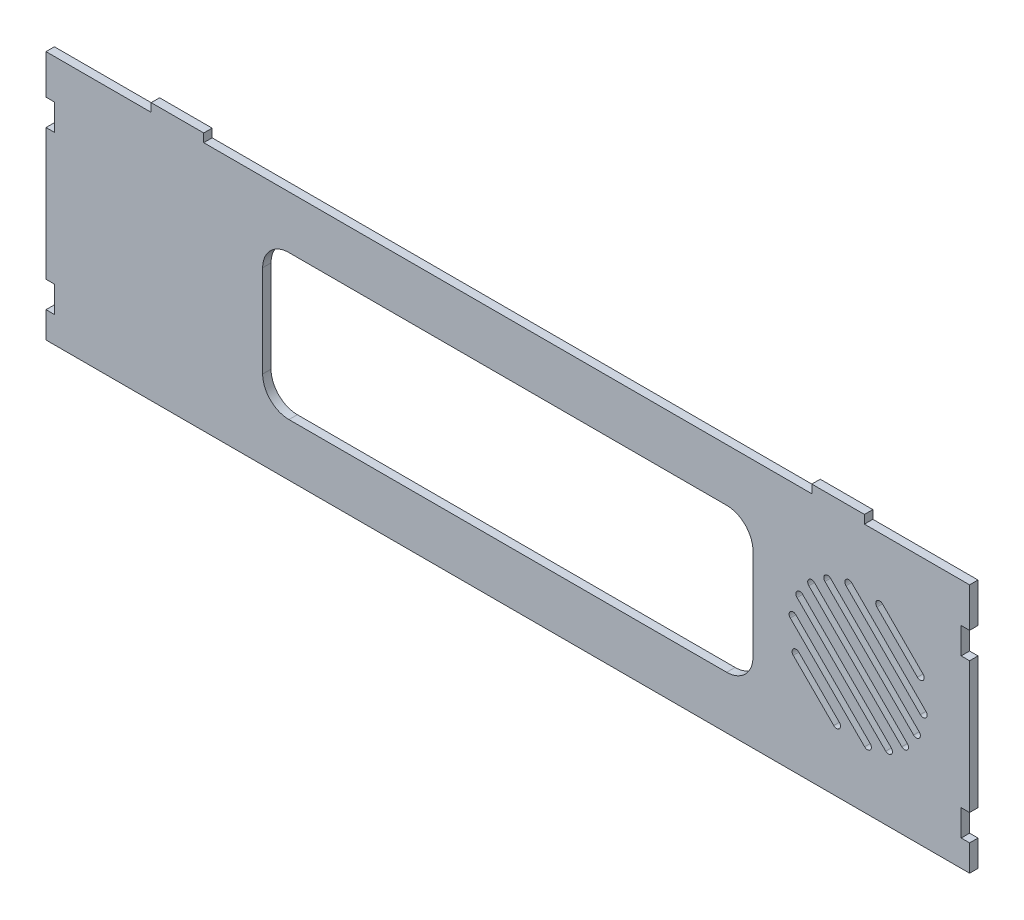
SolidWorks part; units mm, degrees
ref_plane "Front Plane" through (0, 0, 0) normal (0, 0, 1) x (1, 0, 0)
ref_plane "Top Plane" through (0, 0, 0) normal (0, 1, 0) x (1, 0, 0)
ref_plane "Right Plane" through (0, 0, 0) normal (1, 0, 0) x (0, 0, -1)
sketch "Sketch1" plane through (0, 0, 0) normal (0, 0, 1) x (1, 0, 0)
  line L0 (-223.0755, -19.05) -> (-219.0115, -19.05)
  line L1 (-223.0755, 0) -> (-172.2755, 0)
  line L2 (-223.0755, 0) -> (-223.0755, -19.05)
  line L3 (-223.0755, -120.65) -> (223.0755, -120.65)
  line L4 (223.0755, 0) -> (223.0755, -19.05)
  line L5 (-219.0115, -19.05) -> (-219.0115, -31.75)
  line L6 (-219.0115, -31.75) -> (-223.0755, -31.75)
  line L7 (-223.0755, -31.75) -> (-223.0755, -95.25)
  line L8 (-223.0755, -95.25) -> (-219.0115, -95.25)
  line L9 (-219.0115, -95.25) -> (-219.0115, -107.95)
  line L10 (-219.0115, -107.95) -> (-223.0755, -107.95)
  line L11 (223.0755, -19.05) -> (219.0115, -19.05)
  line L12 (219.0115, -19.05) -> (219.0115, -31.75)
  line L13 (219.0115, -31.75) -> (223.0755, -31.75)
  line L14 (223.0755, -95.25) -> (219.0115, -95.25)
  line L15 (219.0115, -95.25) -> (219.0115, -107.95)
  line L16 (219.0115, -107.95) -> (223.0755, -107.95)
  line L17 (-223.0755, -107.95) -> (-223.0755, -120.65)
  line L18 (223.0755, -107.95) -> (223.0755, -120.65)
  line L19 (223.0755, -31.75) -> (223.0755, -95.25)
  line L20 (223.0755, 4.064) -> (223.0755, 0) construction
  line L21 (-118.4275, -120.65) -> (-223.0755, -120.65) construction
  line L22 (-146.8755, 4.064) -> (-146.8755, 0) construction
  line L23 (-146.8755, 0) -> (146.8755, 0)
  line L24 (172.2755, 0) -> (172.2755, 4.064)
  line L25 (172.2755, 4.064) -> (146.8755, 4.064)
  line L26 (146.8755, 0) -> (146.8755, 4.064)
  line L28 (-146.8755, 0) -> (-146.8755, 4.064)
  line L29 (-146.8755, 4.064) -> (-172.2755, 4.064)
  line L30 (-172.2755, 0) -> (-172.2755, 4.064)
  line L31 (172.2755, 4.064) -> (172.2755, 0) construction
  line L32 (172.2755, 0) -> (223.0755, 0)
  line L33 (-93.1545, 0) -> (-219.0115, 0) construction
  dimension "D1" = 12.7
  dimension "D2" = 19.05
  dimension "D3" = 12.7
  dimension "D4" = 12.7
  dimension "D5" = 4.064
  dimension "D6" = 4.064
  dimension "D7" = 4.064
  dimension "D8" = 4.064
extrude "Boss-Extrude1" add sketch "Sketch1" along normal blind 4.064
sketch "Sketch2" plane through (0, 0, 4.064) normal (0, 0, 1) x (1, 0, 0)
  line L0 (146.7769, -37.8744) -> (191.6781, -82.7756) construction
  line L1 (-105.7275, -25.4) -> (105.7275, -25.4)
  line L2 (-118.4275, -38.1) -> (-118.4275, -82.55)
  line L3 (-105.7275, -95.25) -> (105.7275, -95.25)
  line L4 (118.4275, -38.1) -> (118.4275, -82.55)
  line L5 (154.5461, -32.1733) -> (197.3792, -75.0064) construction
  line L6 (200.6584, -64.8151) -> (164.7374, -28.8941) construction
  line L7 (141.0758, -45.6436) -> (183.9089, -88.4767) construction
  line L8 (173.7176, -91.7559) -> (137.7966, -55.8349) construction
  line L9 (179.6471, -30.3334) -> (199.2191, -49.9054) construction
  line L10 (139.2359, -70.7446) -> (158.8079, -90.3166) construction
  line L11 (207.4849, 0) -> (207.4849, -120.65) construction
  line L12 (-172.2755, 0) -> (-223.0755, 0) construction
  line L13 (-223.0755, -120.65) -> (223.0755, -120.65) construction
  line L14 (137.8889, -72.0916) -> (157.4609, -91.6636)
  line L15 (175.0647, -90.4089) -> (139.1436, -54.4878)
  line L16 (139.7287, -46.9907) -> (182.5618, -89.8238)
  line L17 (145.4298, -39.2214) -> (190.3311, -84.1227)
  line L18 (153.1991, -33.5203) -> (196.0322, -76.3534)
  line L19 (202.0054, -63.4681) -> (166.0844, -27.5471)
  line L20 (178.3, -31.6805) -> (197.872, -51.2525)
  line L21 (140.583, -69.3975) -> (160.155, -88.9695)
  line L22 (172.3706, -93.1029) -> (136.4496, -57.1819)
  line L23 (142.4228, -44.2966) -> (185.2559, -87.1297)
  line L24 (148.1239, -36.5273) -> (193.0252, -81.4286)
  line L25 (155.8932, -30.8262) -> (198.7263, -73.6593)
  line L26 (199.3114, -66.1622) -> (163.3903, -30.2411)
  line L27 (180.9941, -28.9864) -> (200.5661, -48.5584)
  line L28 (-118.4275, -120.65) -> (-118.4275, -123.063) construction
  line L29 (223.0755, -95.25) -> (223.0755, -31.75) construction
  circle A0 centre (169.2275, -60.325) radius 31.75 construction
  arc A1 (137.8889, -72.0916) -> (140.583, -69.3975) centre (139.2359, -70.7446) cw
  arc A2 (157.4609, -91.6636) -> (160.155, -88.9695) centre (158.8079, -90.3166) ccw
  arc A3 (175.0647, -90.4089) -> (172.3706, -93.1029) centre (173.7176, -91.7559) cw
  arc A4 (139.1436, -54.4878) -> (136.4496, -57.1819) centre (137.7966, -55.8349) ccw
  arc A5 (139.7287, -46.9907) -> (142.4228, -44.2966) centre (141.0758, -45.6436) cw
  arc A6 (182.5618, -89.8238) -> (185.2559, -87.1297) centre (183.9089, -88.4767) ccw
  arc A7 (145.4298, -39.2214) -> (148.1239, -36.5273) centre (146.7769, -37.8744) cw
  arc A8 (190.3311, -84.1227) -> (193.0252, -81.4286) centre (191.6781, -82.7756) ccw
  arc A9 (153.1991, -33.5203) -> (155.8932, -30.8262) centre (154.5461, -32.1733) cw
  arc A10 (196.0322, -76.3534) -> (198.7263, -73.6593) centre (197.3792, -75.0064) ccw
  arc A11 (202.0054, -63.4681) -> (199.3114, -66.1622) centre (200.6584, -64.8151) cw
  arc A12 (166.0844, -27.5471) -> (163.3903, -30.2411) centre (164.7374, -28.8941) ccw
  arc A13 (178.3, -31.6805) -> (180.9941, -28.9864) centre (179.6471, -30.3334) cw
  arc A14 (197.872, -51.2525) -> (200.5661, -48.5584) centre (199.2191, -49.9054) ccw
  arc A15 (105.7275, -25.4) -> (118.4275, -38.1) centre (105.7275, -38.1) cw
  arc A16 (105.7275, -95.25) -> (118.4275, -82.55) centre (105.7275, -82.55) ccw
  arc A17 (-118.4275, -82.55) -> (-105.7275, -95.25) centre (-105.7275, -82.55) ccw
  arc A18 (-105.7275, -25.4) -> (-118.4275, -38.1) centre (-105.7275, -38.1) ccw
  point P8 (169.2275, -60.325)
  point P27 (207.4849, -60.325)
  point P56 (118.4275, -60.325)
  point P57 (0, -25.4)
  dimension "D7" = 63.5
  dimension "D13" = 12.7
  dimension "D1" = 9.525
  dimension "D2" = 9.525
  dimension "D3" = 9.525
  dimension "D4" = 9.525
  dimension "D5" = 9.525
  dimension "D6" = 9.525
  dimension "D10" = 25.4
  dimension "D11" = 50.8
  dimension "D12" = 45
  dimension "D8" = 1.905
  dimension "D9" = 1.905
extrude "Cut-Extrude1" cut sketch "Sketch2" against normal blind 5.08
